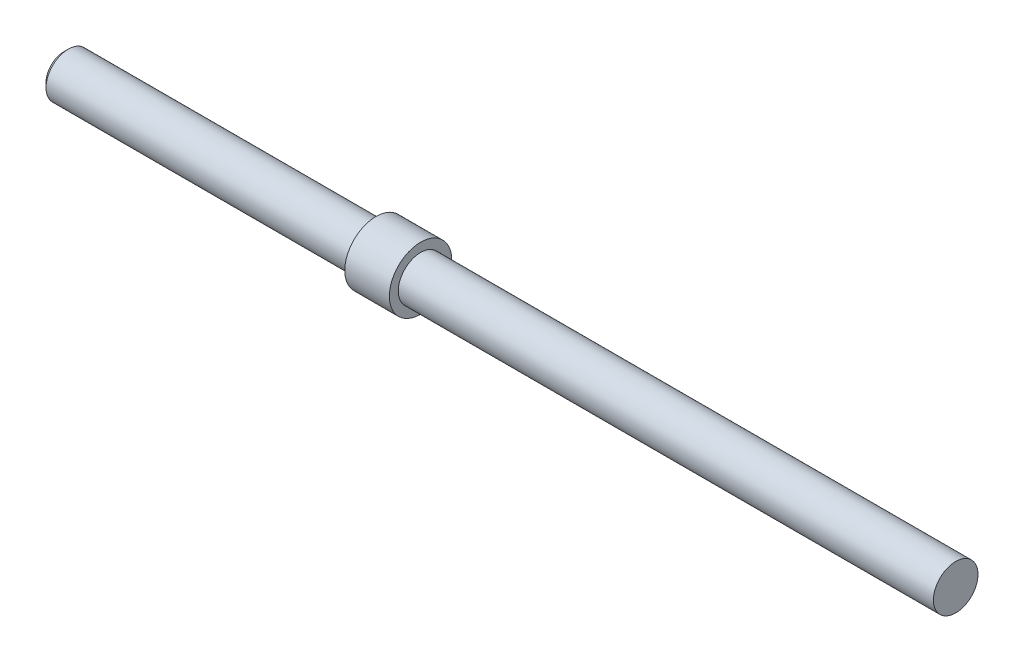
SolidWorks part; units mm, degrees
ref_plane "Front Plane" through (0, 0, 0) normal (0, 0, 1) x (1, 0, 0)
ref_plane "Top Plane" through (0, 0, 0) normal (0, 1, 0) x (1, 0, 0)
ref_plane "Right Plane" through (0, 0, 0) normal (1, 0, 0) x (0, 0, -1)
sketch "Sketch1" plane through (0, 0, 0) normal (1, 0, 0) x (0, 0, -1)
  circle A0 centre (0, 0) radius 5
  dimension "D1" = 10
extrude "Boss-Extrude1" add sketch "Sketch1" along normal blind 200
chamfer "Chamfer1" distance 1 angle 45 1 edges at (0, 0, -5)
sketch "Sketch2" plane through (0, 0, 0) normal (1, 0, 0) x (0, 0, -1)
  circle A0 centre (0, 0) radius 7
  dimension "D1" = 14
extrude "Boss-Extrude2" add sketch "Sketch2" along normal blind 10 from offset 70
